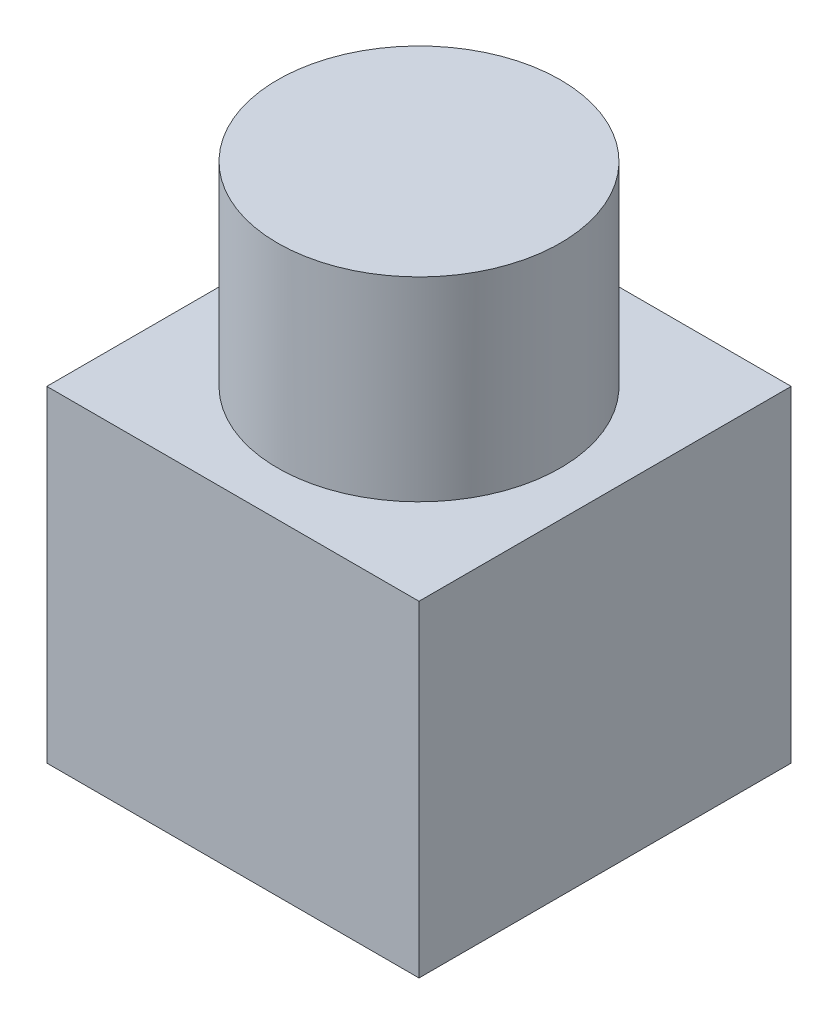
SolidWorks part; units mm, degrees
ref_plane "Front" through (0, 0, 0) normal (0, 0, 1) x (1, 0, 0)
ref_plane "Top" through (0, 0, 0) normal (0, 1, 0) x (1, 0, 0)
ref_plane "Right" through (0, 0, 0) normal (1, 0, 0) x (0, 0, -1)
sketch "Sketch2" plane through (0, 0, 0) normal (0, 1, 0) x (1, 0, 0)
  line L1 (-38.1, -38.1) -> (38.1, -38.1)
  line L2 (-38.1, -38.1) -> (-38.1, 38.1)
  line L3 (-38.1, 38.1) -> (38.1, 38.1)
  line L4 (38.1, -38.1) -> (38.1, 38.1)
  line L5 (-38.1, -38.1) -> (38.1, 38.1) construction
  line L6 (-38.1, 38.1) -> (38.1, -38.1) construction
  point P0 (0, 0)
  dimension "D1" = 76.2
  dimension "D2" = 76.2
extrude "Boss-Extrude1" add sketch "Sketch2" along normal blind 66.802
sketch "Sketch3" plane through (0, 66.802, 0) normal (0, 1, 0) x (1, 0, 0)
  circle A0 centre (0, 0) radius 28.956
  dimension "D1" = 57.912
extrude "Boss-Extrude2" add sketch "Sketch3" along normal blind 39.878
